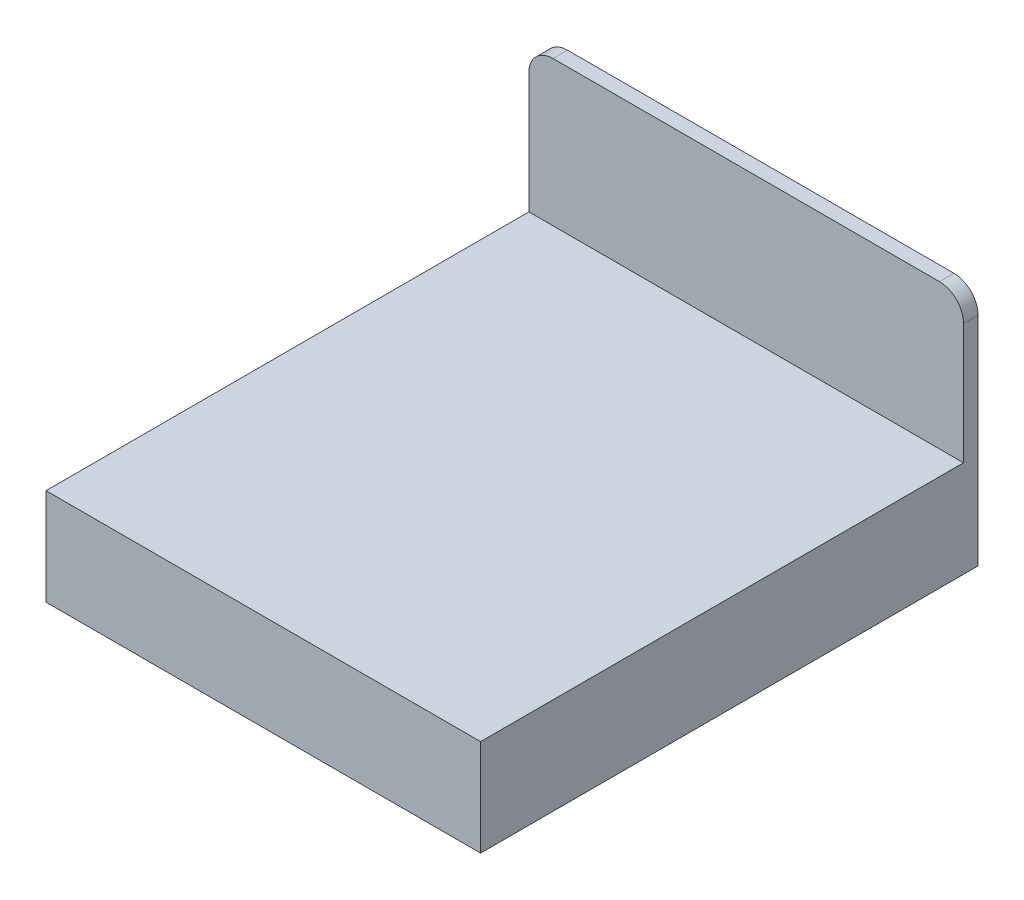
SolidWorks part; units mm, degrees
material "红木"
ref_plane "前视基准面" through (0, 0, 0) normal (0, 0, 1) x (1, 0, 0)
ref_plane "上视基准面" through (0, 0, 0) normal (0, 1, 0) x (1, 0, 0)
ref_plane "右视基准面" through (0, 0, 0) normal (1, 0, 0) x (0, 0, -1)
sketch "草图1" plane through (0, 0, 0) normal (0, 1, 0) x (1, 0, 0)
  line L1 (0, 0) -> (-1800, 0)
  line L2 (0, 0) -> (0, -2000)
  line L3 (0, -2000) -> (-1800, -2000)
  line L4 (-1800, 0) -> (-1800, -2000)
  dimension "D1" = 2000
  dimension "D2" = 1800
extrude "凸台-拉伸1" add sketch "草图1" against normal blind 400
sketch "草图2" plane through (0, 0, 0) normal (0, 0, -1) x (-1, 0, 0)
  line L1 (1800, -400) -> (0, -400) construction
  line L3 (1800, -400) -> (1800, 500)
  line L4 (1800, -400) -> (0, -400)
  line L5 (0, -400) -> (0, 500)
  line L6 (1700, 600) -> (100, 600)
  line L7 (1800, 0) -> (0, 0) construction
  arc A0 (1800, 500) -> (1700, 600) centre (1700, 500) ccw
  arc A1 (100, 600) -> (0, 500) centre (100, 500) ccw
  dimension "D2" = 100
  dimension "D1" = 600
extrude "凸台-拉伸2" add sketch "草图2" along normal blind 60
